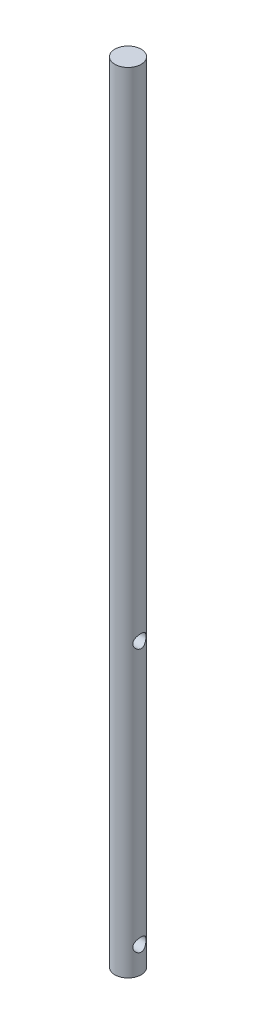
SolidWorks part; units mm, degrees
ref_plane "Спереди" through (0, 0, 0) normal (0, 0, 1) x (1, 0, 0)
ref_plane "Сверху" through (0, 0, 0) normal (0, 1, 0) x (1, 0, 0)
ref_plane "Справа" through (0, 0, 0) normal (1, 0, 0) x (0, 0, -1)
sketch "Эскиз1" plane through (0, 0, 0) normal (1, 0, 0) x (0, 0, -1)
  line L1 (0, 0) -> (5, 0)
  line L2 (0, 0) -> (0, 300)
  line L3 (0, 300) -> (5, 300)
  line L4 (5, 0) -> (5, 300)
revolve "Повернуть1" add sketch "Эскиз1" angle 360 about L2
sketch "Эскиз2" plane through (0, 0, 0) normal (1, 0, 0) x (0, 0, -1)
  circle A0 centre (0, 10) radius 2.5
  circle A1 centre (0, 110) radius 2.5
  dimension "D1" = 2
extrude "Вырез-Вытянуть1" cut sketch "Эскиз2" against normal through all both and the other way through all
